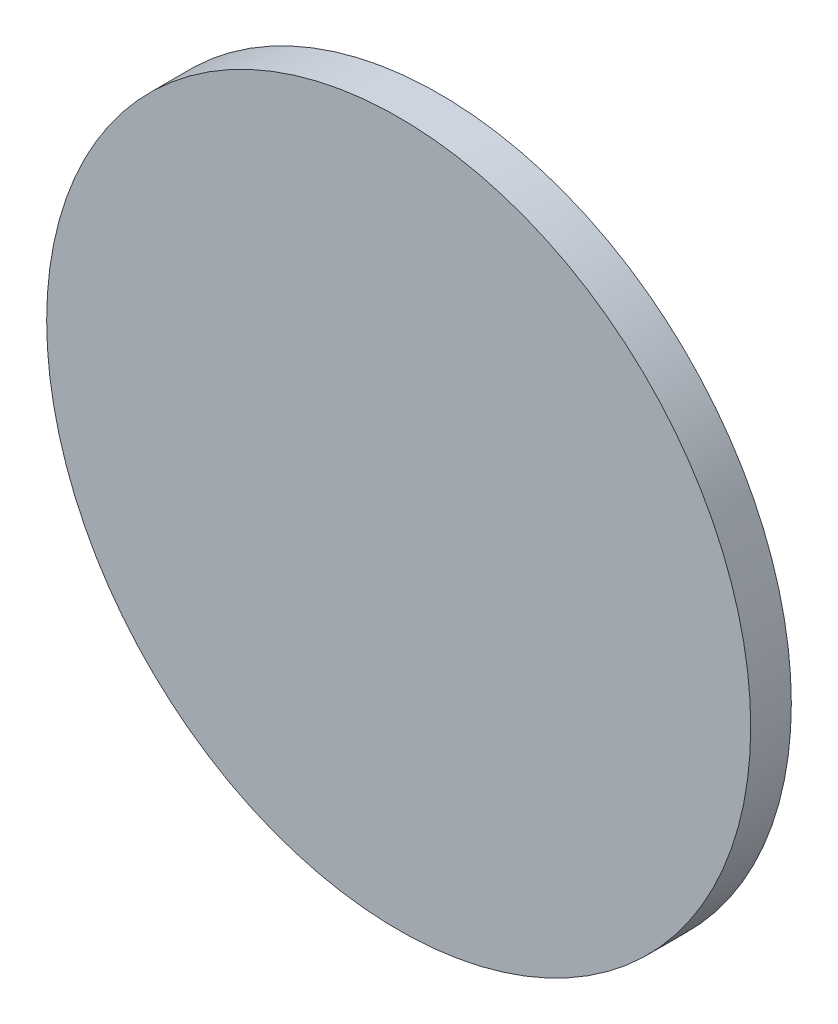
SolidWorks part; units mm, degrees
ref_plane "Front Plane" through (0, 0, 0) normal (0, 0, 1) x (1, 0, 0)
ref_plane "Top Plane" through (0, 0, 0) normal (0, 1, 0) x (1, 0, 0)
ref_plane "Right Plane" through (0, 0, 0) normal (1, 0, 0) x (0, 0, -1)
sketch "Sketch1" plane through (0, 0, 0) normal (0, 0, 1) x (1, 0, 0)
  circle A0 centre (0, 0) radius 330.2
  dimension "D1" = 660.4
extrude "Boss-Extrude1" add sketch "Sketch1" along normal blind 38.1
